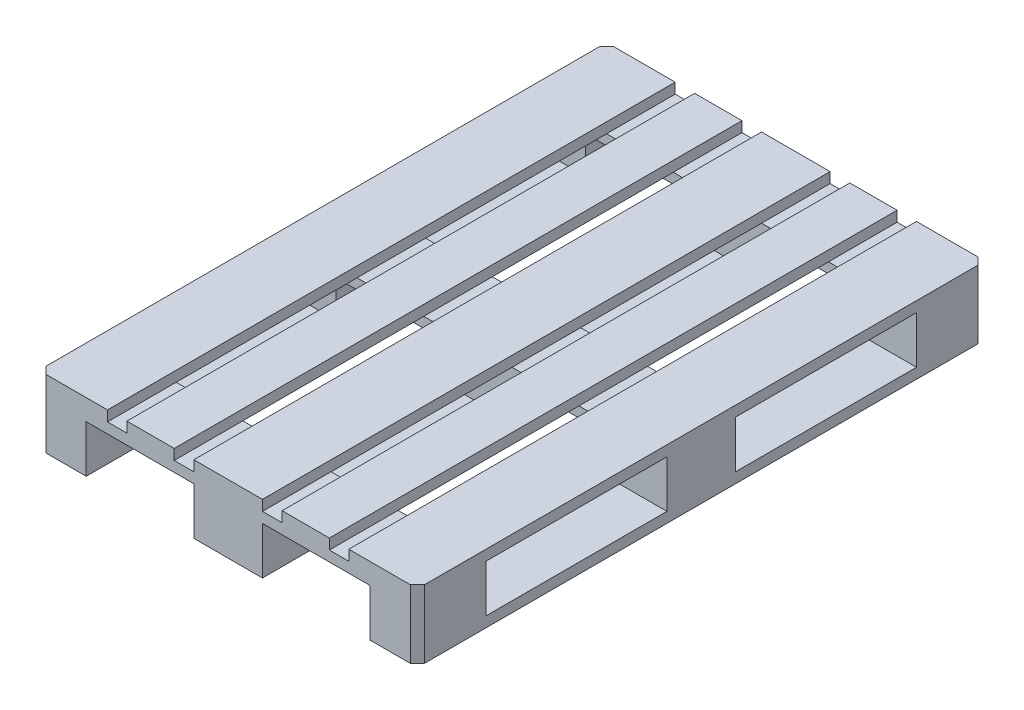
SolidWorks part; units mm, degrees
material "PLA"
ref_plane "Piano frontale" through (0, 0, 0) normal (0, 0, 1) x (1, 0, 0)
ref_plane "Piano superiore" through (0, 0, 0) normal (0, 1, 0) x (1, 0, 0)
ref_plane "Piano destro" through (0, 0, 0) normal (1, 0, 0) x (0, 0, -1)
sketch "Schizzo1" plane through (0, 0, 0) normal (1, 0, 0) x (0, 0, -1)
  line L0 (0, 0) -> (0, 7.2)
  line L1 (0, 7.2) -> (60, 7.2)
  line L2 (60, 7.2) -> (60, 0)
  line L3 (60, 0) -> (0, 0)
  line L8 (33.625, 6.1) -> (33.625, 1.1)
  line L9 (33.625, 1.1) -> (52.75, 1.1)
  line L10 (52.75, 1.1) -> (52.75, 6.1)
  line L11 (52.75, 6.1) -> (33.625, 6.1)
  line L12 (30, 7.2) -> (30, 0) construction
  line L13 (7.25, 1.1) -> (7.25, 6.1)
  line L14 (26.375, 1.1) -> (7.25, 1.1)
  line L15 (26.375, 6.1) -> (26.375, 1.1)
  line L16 (7.25, 6.1) -> (26.375, 6.1)
  dimension "D1" = 7.2
  dimension "D2" = 7.25
  dimension "D3" = 5
  dimension "D4" = 7.25
  dimension "D5" = 60
  dimension "D6" = 1.1
extrude "Estrusione-Estrusione1" add sketch "Schizzo1" along normal blind 40
sketch "Schizzo2" plane through (0, 0, 0) normal (0, 0, 1) x (1, 0, 0)
  line L0 (5, 0) -> (5, 5)
  line L1 (40, 0) -> (0, 0) construction
  line L2 (5, 5) -> (16.375, 5)
  line L3 (16.375, 5) -> (16.375, 0)
  line L4 (16.375, 0) -> (5, 0)
  line L5 (20, 7.2) -> (20, 0) construction
  line L6 (40, 7.2) -> (0, 7.2) construction
  line L8 (0, 7.2) -> (0, 0) construction
  line L9 (23.625, 5) -> (23.625, 0)
  line L14 (14.3, 7.2) -> (16.375, 7.2)
  line L15 (14.3, 7.2) -> (14.3, 6.1)
  line L16 (14.3, 6.1) -> (16.375, 6.1)
  line L17 (16.375, 7.2) -> (16.375, 6.1)
  line L18 (7.25, 7.2) -> (9.3, 7.2)
  line L19 (7.25, 7.2) -> (7.25, 6.1)
  line L20 (7.25, 6.1) -> (9.3, 6.1)
  line L21 (9.3, 7.2) -> (9.3, 6.1)
  line L22 (35, 5) -> (23.625, 5)
  line L23 (35, 0) -> (35, 5)
  line L24 (23.625, 0) -> (35, 0)
  line L25 (25.7, 6.1) -> (23.625, 6.1)
  line L26 (23.625, 7.2) -> (23.625, 6.1)
  line L27 (25.7, 7.2) -> (23.625, 7.2)
  line L28 (25.7, 7.2) -> (25.7, 6.1)
  line L29 (32.75, 6.1) -> (30.7, 6.1)
  line L30 (30.7, 7.2) -> (30.7, 6.1)
  line L31 (32.75, 7.2) -> (30.7, 7.2)
  line L32 (32.75, 7.2) -> (32.75, 6.1)
  dimension "D1" = 5
  dimension "D2" = 3.625
  dimension "D3" = 2.2
  dimension "D4" = 1.1
  dimension "D5" = 7.25
  dimension "D6" = 3.625
  dimension "D7" = 21.4
  dimension "D8" = 1.1
  dimension "D9" = 5
extrude "Taglio-Estrusione1" cut sketch "Schizzo2" against normal through all
chamfer "Smusso1" distance 0.75 angle 45 4 edges at (0, 3.6, -60) (40, 3.6, -60) (40, 3.6, 0) (0, 3.6, 0)
